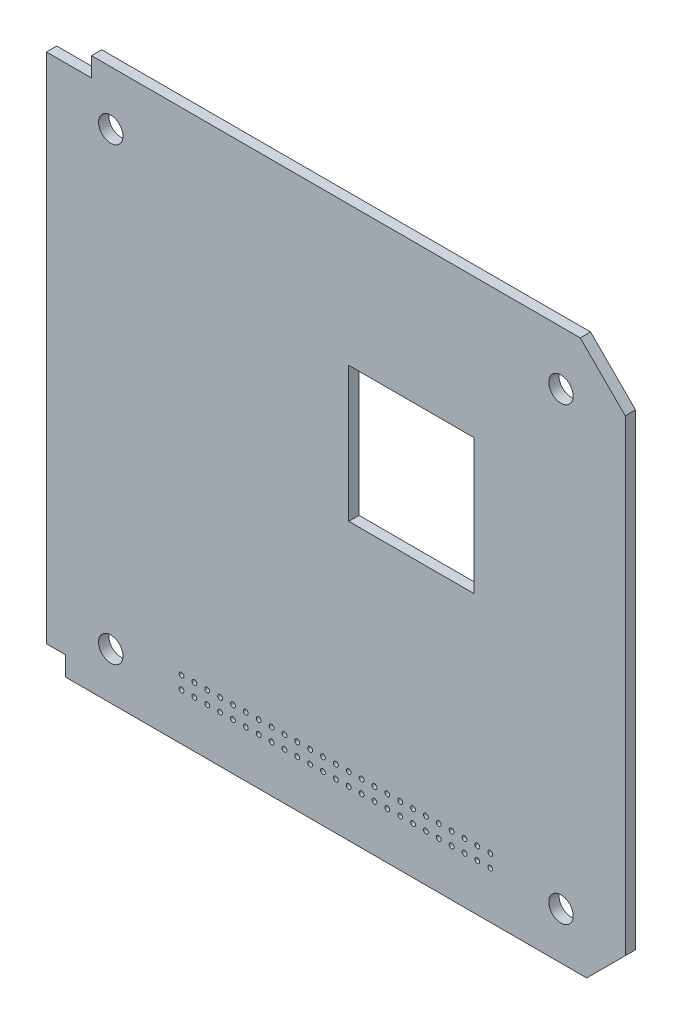
SolidWorks part; units mm, degrees
material "電力回路基板"
ref_plane "Front Plane" through (0, 0, 0) normal (0, 0, 1) x (1, 0, 0)
ref_plane "Top Plane" through (0, 0, 0) normal (0, 1, 0) x (1, 0, 0)
ref_plane "Right Plane" through (0, 0, 0) normal (1, 0, 0) x (0, 0, -1)
sketch "Sketch1" plane through (0, 0, 0) normal (0, 0, 1) x (1, 0, 0)
  line L0 (90, -79.7) -> (90, 0)
  line L1 (0, 0) -> (90, 0)
  line L2 (90, -79.7) -> (84, -85.7)
  line L11 (0, -82.7) -> (3, -82.7)
  line L12 (3, -85.7) -> (3, -82.7)
  line L13 (84, -85.7) -> (3, -85.7)
  line L14 (0, -82.7) -> (0, 0)
  circle A0 centre (10, -78.4) radius 1.9
  circle A1 centre (10, -8.4) radius 1.9
  circle A2 centre (80, -8.4) radius 1.9
  circle A3 centre (80, -78.4) radius 1.9
  circle A4 centre (21, -76.4) radius 0.375
  circle A5 centre (23, -76.4) radius 0.375
  circle A6 centre (25, -76.4) radius 0.375
  circle A7 centre (27, -76.4) radius 0.375
  circle A8 centre (29, -76.4) radius 0.375
  circle A9 centre (31, -76.4) radius 0.375
  circle A10 centre (33, -76.4) radius 0.375
  circle A11 centre (35, -76.4) radius 0.375
  circle A12 centre (37, -76.4) radius 0.375
  circle A13 centre (39, -76.4) radius 0.375
  circle A14 centre (41, -76.4) radius 0.375
  circle A15 centre (43, -76.4) radius 0.375
  circle A16 centre (45, -76.4) radius 0.375
  circle A17 centre (47, -76.4) radius 0.375
  circle A18 centre (49, -76.4) radius 0.375
  circle A19 centre (51, -76.4) radius 0.375
  circle A20 centre (53, -76.4) radius 0.375
  circle A21 centre (55, -76.4) radius 0.375
  circle A22 centre (57, -76.4) radius 0.375
  circle A23 centre (59, -76.4) radius 0.375
  circle A24 centre (61, -76.4) radius 0.375
  circle A25 centre (63, -76.4) radius 0.375
  circle A26 centre (65, -76.4) radius 0.375
  circle A27 centre (67, -76.4) radius 0.375
  circle A28 centre (69, -76.4) radius 0.375
  circle A29 centre (23, -78.4) radius 0.375
  circle A30 centre (25, -78.4) radius 0.375
  circle A31 centre (27, -78.4) radius 0.375
  circle A32 centre (29, -78.4) radius 0.375
  circle A33 centre (31, -78.4) radius 0.375
  circle A34 centre (33, -78.4) radius 0.375
  circle A35 centre (35, -78.4) radius 0.375
  circle A36 centre (37, -78.4) radius 0.375
  circle A37 centre (39, -78.4) radius 0.375
  circle A38 centre (41, -78.4) radius 0.375
  circle A39 centre (43, -78.4) radius 0.375
  circle A40 centre (45, -78.4) radius 0.375
  circle A41 centre (47, -78.4) radius 0.375
  circle A42 centre (49, -78.4) radius 0.375
  circle A43 centre (51, -78.4) radius 0.375
  circle A44 centre (53, -78.4) radius 0.375
  circle A45 centre (55, -78.4) radius 0.375
  circle A46 centre (57, -78.4) radius 0.375
  circle A47 centre (59, -78.4) radius 0.375
  circle A48 centre (61, -78.4) radius 0.375
  circle A49 centre (63, -78.4) radius 0.375
  circle A50 centre (65, -78.4) radius 0.375
  circle A51 centre (67, -78.4) radius 0.375
  circle A52 centre (69, -78.4) radius 0.375
  circle A53 centre (21, -78.4) radius 0.375
  dimension "D2" = 3.8
  dimension "D3" = 3.8
  dimension "D13" = 10
  dimension "D14" = 25
  dimension "D15" = 2
  dimension "D16" = 7.3
  dimension "D17" = 21
  dimension "D4" = 70
  dimension "D5" = 7.3
  dimension "D6" = 90
  dimension "D7" = 70
  dimension "D8" = 85.7
  dimension "D11" = 3
  dimension "D12" = 3
extrude "Boss-Extrude1" add sketch "Sketch1" along normal blind 1.6
sketch "Sketch3" plane through (0, 0, 1.6) normal (0, 0, 1) x (1, 0, 0)
  circle A0 centre (10, -78.4) radius 3
  circle A1 centre (80, -78.4) radius 3
  circle A2 centre (10, -8.4) radius 3
  circle A3 centre (80, -8.4) radius 3
sketch "ｽｹｯﾁ1" plane through (0, 0, 1.6) normal (0, 0, 1) x (1, 0, 0)
  line L0 (90, 0) -> (0, 0) construction
  line L1 (66.5, -21.7) -> (47, -21.7)
  line L2 (66.5, -21.7) -> (66.5, -42.7)
  line L3 (66.5, -42.7) -> (47, -42.7)
  line L4 (47, -21.7) -> (47, -42.7)
  line L5 (90, -79.7) -> (90, 0) construction
  dimension "D1" = 21.7
  dimension "D2" = 23.5
extrude "ｶｯﾄ - 押し出し1" cut sketch "ｽｹｯﾁ1" against normal blind 10
sketch "ｽｹｯﾁ2" plane through (0, 0, 1.6) normal (0, 0, 1) x (1, 0, 0)
  line L0 (90, 0) -> (90, -7)
  line L1 (90, -7) -> (83, 0)
  line L2 (83, 0) -> (90, 0)
  line L3 (0, 0) -> (7, 0)
  line L4 (7, 0) -> (7, -3)
  line L5 (7, -3) -> (0, -3)
  line L6 (0, -3) -> (0, 0)
extrude "ｶｯﾄ - 押し出し2" cut sketch "ｽｹｯﾁ2" against normal blind 10
